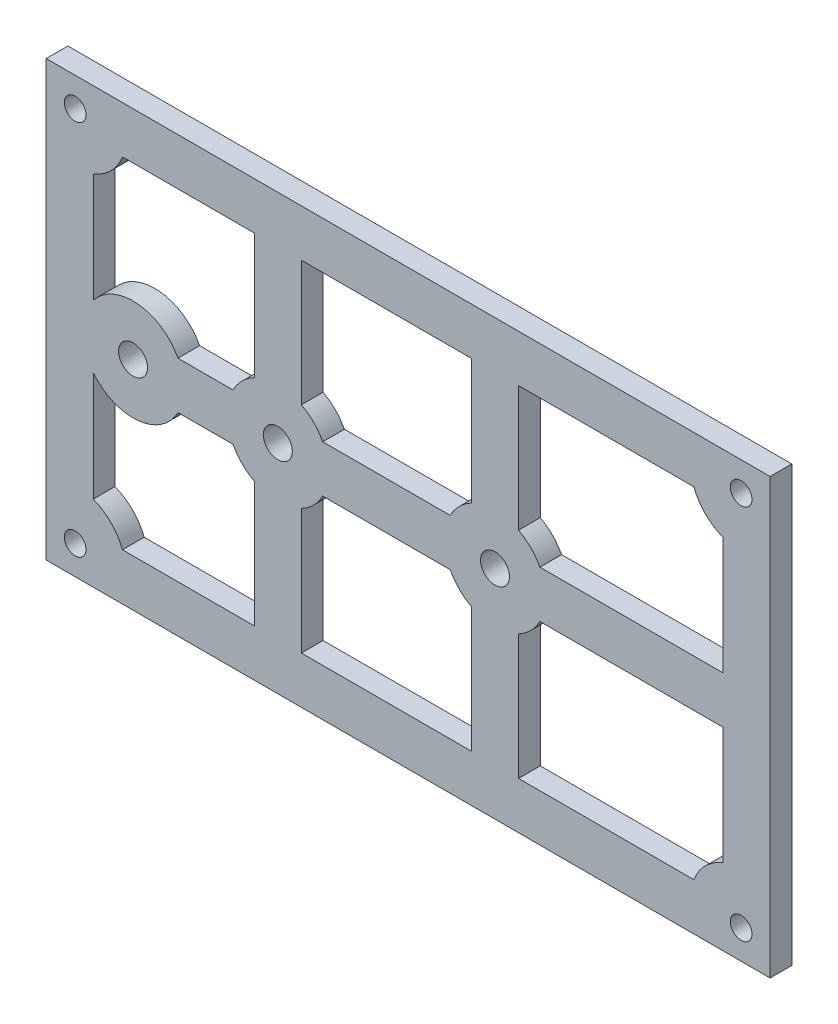
SolidWorks part; units mm, degrees
ref_plane "Front Plane" through (0, 0, 0) normal (0, 0, 1) x (1, 0, 0)
ref_plane "Top Plane" through (0, 0, 0) normal (0, 1, 0) x (1, 0, 0)
ref_plane "Right Plane" through (0, 0, 0) normal (1, 0, 0) x (0, 0, -1)
sketch "Sketch1" plane through (0, 0, 0) normal (0, 0, 1) x (1, 0, 0)
  line L1 (-50, 30) -> (50, 30)
  line L2 (-50, 30) -> (-50, -30)
  line L3 (-50, -30) -> (50, -30)
  line L4 (50, 30) -> (50, -30)
  line L5 (-50, 30) -> (50, -30) construction
  line L6 (-50, -30) -> (50, 30) construction
  point P0 (0, 0)
  dimension "D1" = 100
  dimension "D2" = 60
extrude "Boss-Extrude1" add sketch "Sketch1" along normal blind 3
sketch "Sketch2" plane through (0, 0, 3) normal (0, 0, 1) x (1, 0, 0)
  line L0 (50, 30) -> (-50, 30) construction
  line L1 (-50, -30) -> (50, -30) construction
  line L2 (-50, 30) -> (-50, -30) construction
  line L3 (50, -30) -> (50, 30) construction
  circle A0 centre (-38, 0) radius 2
  circle A1 centre (-18, 0) radius 2
  circle A2 centre (12, 0) radius 2
  circle A3 centre (-46, 26) radius 1.5
  circle A4 centre (46, 26) radius 1.5
  circle A5 centre (46, -26) radius 1.5
  circle A6 centre (-46, -26) radius 1.5
  dimension "D1" = 4
  dimension "D2" = 4
  dimension "D3" = 4
  dimension "D4" = 30
  dimension "D5" = 20
  dimension "D6" = 30
  dimension "D7" = 12
  dimension "D8" = 3
  dimension "D9" = 4
  dimension "D10" = 4
  dimension "D11" = 3
  dimension "D12" = 3
  dimension "D13" = 3
  dimension "D14" = 4
  dimension "D15" = 4
  dimension "D16" = 4
  dimension "D17" = 4
  dimension "D18" = 4
  dimension "D19" = 4
extrude "Cut-Extrude1" cut sketch "Sketch2" against normal blind 3
sketch "Sketch3" plane through (0, 0, 3) normal (0, 0, 1) x (1, 0, 0)
  line L0 (50, 30) -> (-50, 30) construction
  line L1 (-14.75, 23.5) -> (8.75, 23.5)
  line L2 (-14.75, 23.5) -> (-14.75, 3.25)
  line L3 (-14.75, 3.25) -> (8.75, 3.25)
  line L4 (8.75, 23.5) -> (8.75, 3.25)
  line L5 (-14.75, 23.5) -> (8.75, 3.25) construction
  line L6 (-14.75, 3.25) -> (8.75, 23.5) construction
  line L8 (-18, 0) -> (-18, 30) construction
  line L9 (12, 0) -> (12, 30) construction
  point P0 (-3, 13.375)
  dimension "D1" = 20.25
  dimension "D2" = 23.5
  dimension "D3" = 3.25
  dimension "D4" = 6.5
extrude "Cut-Extrude2" cut sketch "Sketch3" against normal blind 10
mirror "Mirror1" about plane through (0, 0, 0) normal (0, 1, 0) of "Cut-Extrude2"
sketch "Sketch4" plane through (0, 0, 3) normal (0, 0, 1) x (1, 0, 0)
  line L0 (50, 30) -> (-50, 30) construction
  line L1 (-39.4617, 23.5) -> (-21.25, 23.5)
  line L2 (-43.5, 19.4617) -> (-43.5, 4.3301)
  line L3 (-31.8002, 3.25) -> (-21.25, 3.25)
  line L4 (-21.25, 23.5) -> (-21.25, 6.1998)
  line L5 (-47.8317, 19.2439) -> (-24.0162, 3.5784) construction
  line L6 (-35.0169, 6.3326) -> (-21.25, 23.5) construction
  line L9 (-18, 0) -> (-18, 30) construction
  arc A0 (-43.5, 4.3301) -> (-31.8002, 3.25) centre (-38, 0) cw
  arc A1 (-43.5, 19.4617) -> (-39.4617, 23.5) centre (-46, 26) ccw
  arc A2 (-24.1998, 3.25) -> (-21.25, 6.1998) centre (-18, 0) cw
  point P0 (-32.6639, 9.2667)
  dimension "D5" = 7
  dimension "D6" = 7
  dimension "D7" = 7
  dimension "D1" = 20.25
  dimension "D2" = 18.2117
  dimension "D3" = 3.25
  dimension "D4" = 10.5502
  dimension "D8" = 15.1315
extrude "Cut-Extrude3" cut sketch "Sketch4" against normal blind 10 contours L3 A2 L4 L1 A1 L2 A0
mirror "Mirror2" about plane through (0, 0, 0) normal (0, 1, 0) of "Cut-Extrude3"
sketch "Sketch5" plane through (0, 0, 3) normal (0, 0, 1) x (1, 0, 0)
  line L0 (50, 30) -> (-50, 30) construction
  line L1 (15.25, 23.5) -> (43.5, 23.5)
  line L2 (15.25, 23.5) -> (15.25, 3.25)
  line L3 (15.25, 3.25) -> (43.5, 3.25)
  line L4 (43.5, 23.5) -> (43.5, 3.25)
  line L5 (15.25, 23.5) -> (43.5, 3.25) construction
  line L6 (15.25, 3.25) -> (43.5, 23.5) construction
  line L7 (8.75, 3.25) -> (8.75, 23.5) construction
  line L8 (50, -30) -> (50, 30) construction
  point P0 (29.375, 13.375)
  dimension "D1" = 20.25
  dimension "D2" = 6.5
  dimension "D3" = 6.5
  dimension "D4" = 6.5
extrude "Cut-Extrude4" cut sketch "Sketch5" against normal blind 10
sketch "Sketch6" plane through (0, 0, 3) normal (0, 0, 1) x (1, 0, 0)
  circle A0 centre (-18, 0) radius 7
  dimension "D1" = 14
extrude "Boss-Extrude2" add sketch "Sketch6" against normal blind 3
sketch "Sketch7" plane through (0, 0, 3) normal (0, 0, 1) x (1, 0, 0)
  circle A0 centre (-18, 0) radius 2
  circle A1 centre (-38, 0) radius 2 construction
  circle A2 centre (12, 0) radius 2 construction
  dimension "D1" = 4
  dimension "D2" = 20
  dimension "D3" = 30
extrude "Cut-Extrude6" cut sketch "Sketch7" against normal blind 3
mirror "Mirror4" about plane through (0, 0, 0) normal (0, 1, 0) of "Cut-Extrude4"
sketch "Sketch9" plane through (0, 0, 3) normal (0, 0, 1) x (1, 0, 0)
  circle A0 centre (12, 0) radius 7
  circle A1 centre (12, 0) radius 2
  dimension "D1" = 14
extrude "Boss-Extrude3" add sketch "Sketch9" against normal blind 3
sketch "Sketch11" plane through (0, 0, 3) normal (0, 0, 1) x (1, 0, 0)
  line L0 (43.5, 3.25) -> (43.5, 23.5) construction
  line L1 (43.5, 23.5) -> (15.25, 23.5) construction
  line L2 (43.5, 19.4617) -> (43.5, 23.5)
  line L3 (43.5, 23.5) -> (39.4617, 23.5)
  arc A0 (43.5, 19.4617) -> (39.4617, 23.5) centre (46, 26) cw
  dimension "D1" = 7
extrude "Boss-Extrude4" add sketch "Sketch11" against normal blind 3
mirror "Mirror5" about plane through (0, 0, 0) normal (0, 1, 0) of "Boss-Extrude4"
